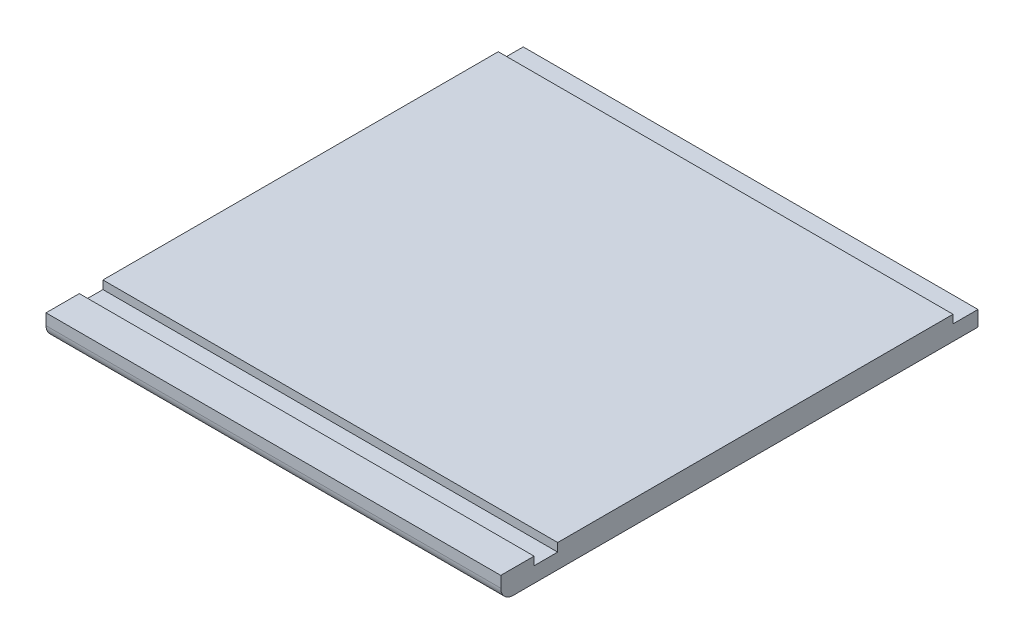
SolidWorks part; units mm, degrees
ref_plane "Front Plane" through (0, 0, 0) normal (0, 0, 1) x (1, 0, 0)
ref_plane "Top Plane" through (0, 0, 0) normal (0, 1, 0) x (1, 0, 0)
ref_plane "Right Plane" through (0, 0, 0) normal (1, 0, 0) x (0, 0, -1)
sketch "Sketch1" plane through (0, 0, 0) normal (0, 1, 0) x (1, 0, 0)
  line L1 (0, 0) -> (346.7, 0)
  line L2 (0, 0) -> (0, -376.55)
  line L3 (0, -376.55) -> (346.7, -376.55)
  line L4 (346.7, 0) -> (346.7, -376.55)
  dimension "D1" = 346.7
  dimension "D2" = 376.55
extrude "Boss-Extrude1" add sketch "Sketch1" along normal blind 18
sketch "Sketch2" plane through (0, 18, 0) normal (0, 1, 0) x (1, 0, 0)
  line L0 (0, -376.55) -> (346.7, -376.55) construction
  line L1 (346.7, -338.45) -> (0, -338.45)
  line L2 (346.7, -338.45) -> (346.7, -320.45)
  line L3 (346.7, -320.45) -> (0, -320.45)
  line L4 (0, -338.45) -> (0, -320.45)
  line L5 (0, 0) -> (0, -376.55) construction
  line L6 (346.7, -376.55) -> (346.7, 0) construction
  dimension "D1" = 18
  dimension "D2" = 38.1
  dimension "D3" = 0
  dimension "D4" = 0
extrude "Cut-Extrude1" cut sketch "Sketch2" against normal blind 6.35
fillet "Fillet1" radius 9.525 1 edges at (173.35, 0, 376.55)
sketch "Sketch3" plane through (0, 18, 0) normal (0, 1, 0) x (1, 0, 0)
  line L0 (346.7, -320.45) -> (346.7, 0) construction
  line L1 (0, 0) -> (346.7, 0)
  line L2 (0, 0) -> (0, -19.05)
  line L3 (0, -19.05) -> (346.7, -19.05)
  line L4 (346.7, 0) -> (346.7, -19.05)
  dimension "D1" = 19.05
extrude "Cut-Extrude2" cut sketch "Sketch3" against normal up to surface (6.35 mm away) up to face at (173.35, 11.65, 329.45)
sketch "Sketch4" plane through (0, 18, 0) normal (0, 1, 0) x (1, 0, 0)
  line L0 (346.7, -376.55) -> (346.7, -338.45) construction
  line L1 (0, -376.55) -> (346.7, -376.55)
  line L2 (0, -376.55) -> (0, -363.85)
  line L3 (0, -363.85) -> (346.7, -363.85)
  line L4 (346.7, -376.55) -> (346.7, -363.85)
  dimension "D1" = 12.7
extrude "Cut-Extrude3" cut sketch "Sketch4" against normal through all
fillet "Fillet2" radius 9.525 1 edges at (173.35, 0, 363.85)
